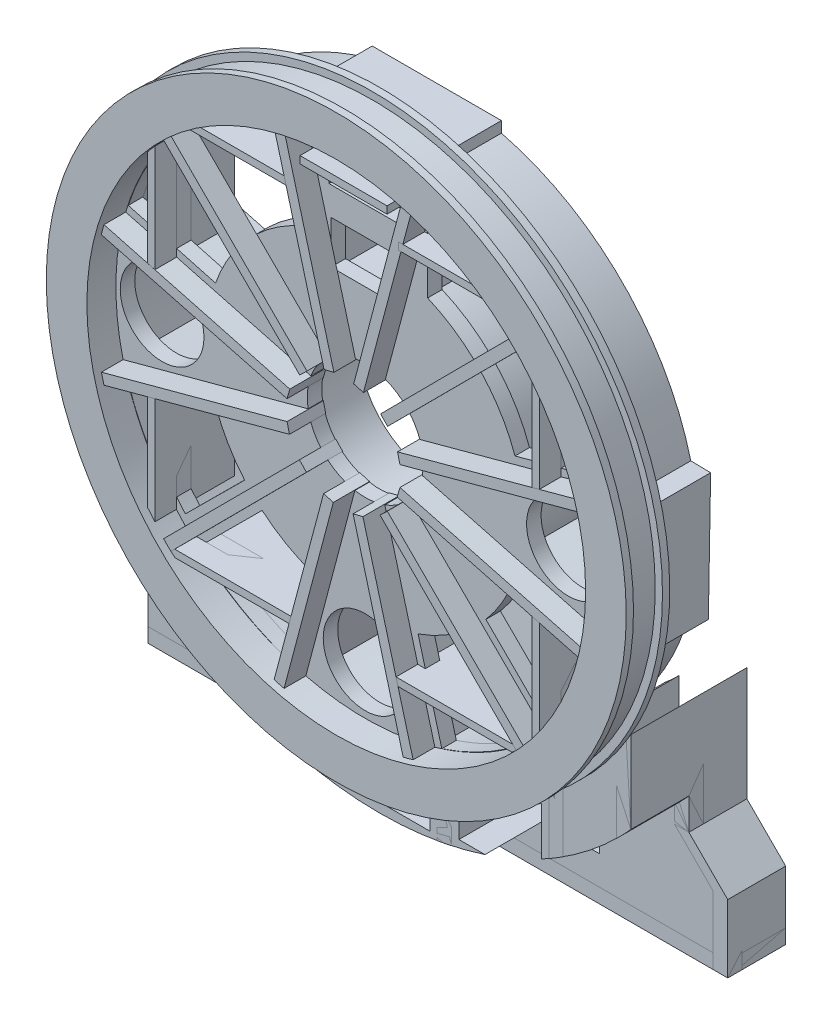
SolidWorks part; units mm, degrees
ref_plane "Front Plane" through (0, 0, 0) normal (0, 0, 1) x (1, 0, 0)
ref_plane "Top Plane" through (0, 0, 0) normal (0, 1, 0) x (1, 0, 0)
ref_plane "Right Plane" through (0, 0, 0) normal (1, 0, 0) x (0, 0, -1)
sketch "Sketch1" plane through (0, 0, 0) normal (0, 0, 1) x (1, 0, 0)
  circle A0 centre (0, 0) radius 200
extrude "Boss-Extrude1" add sketch "Sketch1" along normal blind 5
sketch "Sketch2" plane through (0, 0, 5) normal (0, 0, 1) x (1, 0, 0)
  circle A0 centre (0, 0) radius 195
extrude "Boss-Extrude2" add sketch "Sketch2" along normal blind 10
ref_plane "Plane1" through (0, 0, 15) normal (0, 0, 1) x (1, 0, 0)
mirror "Mirror2" about plane through (0, 0, 15) normal (0, 0, 1) of "Boss-Extrude2"
mirror "Mirror3" about plane through (0, 0, 15) normal (0, 0, 1) of "Boss-Extrude1"
sketch "Sketch4" plane through (0, 0, 0) normal (0, 0, 1) x (1, 0, 0)
  circle A0 centre (0, 0) radius 180
  circle A1 centre (0, 0) radius 172
extrude "Boss-Extrude3" add sketch "Sketch4" against normal blind 40
sketch "Sketch5" plane through (0, 0, 0) normal (0, 0, -1) x (-1, 0, 0)
  circle A0 centre (0, 0) radius 104.5
  circle A1 centre (0, 0) radius 96.5
sketch "Sketch6" plane through (0, 0, 0) normal (0, 0, -1) x (-1, 0, 0)
  circle A0 centre (0, 0) radius 40
extrude "Cut-Extrude1" cut sketch "Sketch6" against normal through all both and the other way through all
sketch "Sketch7" plane through (0, 0, 30) normal (0, 0, 1) x (1, 0, 0)
  circle A0 centre (0, 0) radius 172
  circle A1 centre (0, 0) radius 40 construction
extrude "Cut-Extrude2" cut sketch "Sketch7" against normal blind 20
sketch "Sketch8" plane through (0, 0, 0) normal (0, 0, -1) x (-1, 0, 0)
  line L1 (-226.8867, 0) -> (327.5333, 0) construction
  line L3 (10.3528, -38.637) -> (44.5169, -166.1392) construction
sketch "Sketch11" plane through (0, 0, 0) normal (0, 0, -1) x (-1, 0, 0)
  line L0 (0, 220.657) -> (0, -234.2087) construction
  line L1 (10.3528, -38.637) -> (44.5169, -166.1392) construction
  line L3 (13.739, -37.0329) -> (48.7398, -168.4842) construction
  line L6 (41.8584, -170.3245) -> (7.0358, -38.9499) construction
  line L8 (7.0358, -38.9499) -> (13.739, -37.0329)
  line L9 (7.0358, -38.9499) -> (41.8584, -170.3245)
  line L10 (13.739, -37.0329) -> (48.7398, -168.4842)
  line L11 (41.8584, -170.3245) -> (48.7398, -168.4842)
  dimension "D1" = 15
extrude "Boss-Extrude12" add sketch "Sketch11" along normal blind 40 and the other way blind 25
pattern_circular "CirPattern7" count 12 every 30 about axis through (0, 0, 0) along (0, 0, 1) of "Boss-Extrude12"
extrude "Boss-Extrude14" add sketch "Sketch5" along normal blind 40
sketch "Sketch16" plane through (0, 0, 0) normal (0, 0, -1) x (-1, 0, 0)
  circle A0 centre (0, 0) radius 63
  circle A2 centre (0, 0) radius 55
extrude "Boss-Extrude15" add sketch "Sketch16" along normal blind 40
sketch "Sketch17" plane through (0, 0, 0) normal (0, 0, -1) x (-1, 0, 0)
  circle A0 centre (0, 0) radius 55
  circle A1 centre (0, 0) radius 40
ref_plane "Plane3" through (0, 0, -40) normal (0, 0, -1) x (-1, 0, 0)
sketch "Sketch18" plane through (0, 0, -40) normal (0, 0, -1) x (-1, 0, 0)
  circle A1 centre (0, 0) radius 55
extrude "Cut-Extrude9" cut sketch "Sketch18" against normal blind 40
sketch "Sketch20" plane through (0, 0, 0) normal (0, 0, -1) x (-1, 0, 0)
  line L0 (-76.3832, 71.3152) -> (-124.0564, 119.1386)
  line L1 (76.2988, 71.4055) -> (124.1704, 119.0198)
  line L2 (-70.7313, 65.6455) -> (-47.0532, 41.8927)
  line L3 (70.6239, 65.7611) -> (46.8523, 42.1173)
  arc A0 (76.2988, 71.4055) -> (-76.3832, 71.3152) centre (0, 0) ccw
  arc A1 (124.1704, 119.0198) -> (-124.0564, 119.1386) centre (0, 0) ccw
  arc A2 (46.8523, 42.1173) -> (-47.0532, 41.8927) centre (0, 0) ccw
  arc A3 (70.6239, 65.7611) -> (-70.7313, 65.6455) centre (0, 0) ccw
extrude "Cut-Extrude13" cut sketch "Sketch20" along normal blind 40
sketch "Sketch21" plane through (0, 0, -40) normal (0, 0, -1) x (-1, 0, 0)
  line L0 (0, 245.7288) -> (0, -237.5415) construction
  line L1 (-138.1613, 239.3024) -> (0, 0) construction
  line L2 (0, 0) -> (159.1654, 275.6826) construction
  line L3 (-33.0054, 0) -> (-33.0054, 111.1117) construction
  dimension "D1" = 30
  dimension "D2" = 60
sketch "Sketch22" plane through (0, 0, -40) normal (0, 0, -1) x (-1, 0, 0)
  line L0 (25.0054, 0) -> (25.0054, 281.7628) construction
  line L1 (-25.0054, 0) -> (-25.0054, 250.3344) construction
  line L2 (-33.0054, 0) -> (-33.0054, 111.1117) construction
  line L3 (33.0054, 0) -> (33.0054, 272.1332) construction
  line L4 (-33.0054, 0) -> (-33.0054, 250.3344) construction
  point P11 (-25.0054, 48.987)
  point P12 (-513.0578, 150.8351)
  dimension "D1" = 8
sketch "Sketch25" plane through (0, 0, -40) normal (0, 0, -1) x (-1, 0, 0)
  line L0 (-30.0323, 46.0767) -> (-30.0323, 76.987)
  line L1 (-38.0323, 39.7309) -> (-38.0323, 76.987)
  line L2 (-38.0323, 76.987) -> (38, 76.987)
  line L3 (30, 46.0977) -> (30, 76.987)
  line L4 (-38, 66.987) -> (38, 66.987)
  line L8 (38, 39.7618) -> (38, 76.987)
  line L10 (-30.0323, 176.987) -> (-30.0323, 177.4769)
  line L12 (0, 245.7288) -> (0, -237.5415) construction
  line L13 (0, 130) -> (-38.0323, 130)
  line L16 (38, 130) -> (0, 130)
  line L20 (-38.0323, 76.987) -> (-38.0323, 175.9362)
  line L21 (38, 76.987) -> (38, 175.9432)
  line L22 (30, 76.987) -> (30, 177.4824)
  line L25 (-30.0323, 76.987) -> (-30.0323, 176.987)
  line L26 (-38.0323, 122) -> (38, 122)
  arc A0 (38, 175.9432) -> (-38.0323, 175.9362) centre (0, 0) ccw
  arc A1 (38, 39.7618) -> (30, 46.0977) centre (0, 0) ccw
  arc A2 (-30.0323, 46.0767) -> (-38.0323, 39.7309) centre (0, 0) ccw
  dimension "D1" = 8
  dimension "D4" = 8
  dimension "D2" = 8
extrude "Boss-Extrude18" add sketch "Sketch25" against normal blind 40
sketch "Sketch27" plane through (0, 0, 0) normal (0, 0, -1) x (-1, 0, 0)
  line L1 (-30.0323, 122) -> (30, 122)
  line L2 (-30.0323, 122) -> (-30.0323, 76.987)
  line L3 (-30.0323, 76.987) -> (30, 76.987)
  line L4 (30, 122) -> (30, 76.987)
  line L5 (-30.0323, 122) -> (30, 76.987) construction
  line L6 (-30.0323, 76.987) -> (30, 122) construction
  line L7 (-30.0323, 66.987) -> (30, 66.987)
  line L8 (-30.0323, 66.987) -> (-30.0323, 40)
  line L9 (-30.0323, 40) -> (30, 40)
  line L10 (30, 66.987) -> (30, 40)
  line L11 (-30.0323, 66.987) -> (30, 40) construction
  line L12 (-30.0323, 40) -> (30, 66.987) construction
  point P4 (-0.0161, 99.4935)
  point P11 (-0.0161, 53.4935)
extrude "Cut-Extrude15" cut sketch "Sketch27" along normal blind 40
ref_plane "Plane4" through (0, 0, -50) normal (0, 0, -1) x (-1, 0, 0)
sketch "Sketch30" plane through (0, 0, -50) normal (0, 0, -1) x (-1, 0, 0)
  line L0 (-38.0323, 97.3334) -> (-38.0323, 167.7425) construction
  line L1 (-38.0323, 130) -> (38, 130)
  line L2 (-38.0323, 130) -> (-38.0323, 167.7425)
  line L4 (38, 130) -> (38, 167.7498)
  arc A0 (38, 167.7498) -> (-38.0323, 167.7425) centre (0, 0) ccw
  point P4 (-0.0161, 151.6509)
extrude "Cut-Extrude16" cut sketch "Sketch30" against normal blind 35
ref_plane "Plane5" through (0, 0, -40) normal (0, 0, -1) x (-1, 0, 0)
sketch "Sketch31" plane through (0, 0, -40) normal (0, 0, -1) x (-1, 0, 0)
  line L0 (-38.0323, 167.7425) -> (-38.0323, 182.0805)
  line L1 (-43.8991, 172.6431) -> (-43.8991, 166.3035)
  line L2 (38, 182.0805) -> (38, 167.7498)
  line L3 (-43.8991, 182.0805) -> (45.1952, 182.0805)
  line L8 (-43.8991, 182.0805) -> (-43.8991, 172.6431)
  line L9 (-43.8991, 172.6431) -> (45.1952, 172.6431)
  line L10 (45.1952, 182.0805) -> (45.1952, 172.6431)
  line L11 (45.1952, 172.6431) -> (45.1952, 165.956)
  arc A0 (45.1952, 165.956) -> (-43.8991, 166.3035) centre (0, 0) ccw
  point P10 (-0.0193, 178.6973)
  point P11 (0.648, 177.3618)
extrude "Boss-Extrude19" add sketch "Sketch31" against normal blind 44 contours A0 L0 L9 L1 | L8 L9 L0 L3 | L0 L9 L2 L3 | A0 L2 L9 L0 | A0 L11 L9 L2 | L10 L3 L2 L9
sketch "Sketch32" plane through (0, 0, 0) normal (0, 0, 1) x (1, 0, 0)
  line L0 (0, 0) -> (-173.1406, -99.4798)
  line L1 (0, 0) -> (0, -390) construction
  line L2 (0, 0) -> (173.1482, -99.4666)
  line L3 (173.1482, -99.4666) -> (173.1482, -389.8428)
  line L4 (-173.1406, -99.4798) -> (-173.1406, -389.8428)
  line L5 (0.0076, -199.6845) -> (0, -390)
  line L6 (173.1482, -389.8428) -> (-173.1406, -389.8428)
  line L12 (125.8692, -389.8428) -> (126.5384, -128.0157)
  line L14 (39.5868, -389.8428) -> (39.5868, -195.7212)
  line L16 (49.5868, -389.8428) -> (49.5868, -173.0351)
  line L17 (39.5868, -389.8428) -> (39.5868, -175.593)
  line L19 (-39.4279, -389.8428) -> (-39.4279, -175.6287)
  line L21 (-49.4279, -389.8428) -> (-49.4279, -173.0806)
  line L24 (-116.5381, -389.8428) -> (-116.5381, -137.1819)
  line L26 (-126.5381, -389.8428) -> (-126.5381, -128.016)
  line L28 (116.0868, -389.8428) -> (116.733, -137.0161)
  arc A0 (-173.1406, -99.4798) -> (173.1482, -99.4666) centre (0, 0) ccw
  circle A1 centre (0, 0) radius 180
  point P15 (173.1482, -99.4666)
  point P16 (-173.1406, -99.4798)
extrude "Boss-Extrude20" add sketch "Sketch32" against normal blind 80 contours A0 L28 L6 L12 | A1 L28 A0 L12 | A1 L17 A0 L16 | A0 L14 L6 L16 | A1 L21 A0 L19 | A0 L21 L6 L19 | A1 L26 A0 L24 | A0 L26 L6 L24
sketch "Sketch33" plane through (0, 0, 0) normal (0, 0, -1) x (-1, 0, 0)
  line L2 (0, 0) -> (0, -342.4917) construction
  line L3 (-173.2051, -100) -> (-173.2051, -178.3656)
  line L5 (173.2051, -100) -> (173.2051, -178.6485)
  line L6 (190, -389.8428) -> (190, -205.4434)
  line L7 (-200, -205.1605) -> (-200, -389.8428)
  line L8 (200, -205.4434) -> (200, -389.8428)
  line L9 (-173.2051, -178.3656) -> (-200, -205.1605)
  line L10 (173.2051, -178.6485) -> (200, -205.4434)
  line L13 (190, -389.8428) -> (200, -389.8428)
  line L15 (-190, -389.8428) -> (-190, -205.1605)
  line L16 (-190, -205.1605) -> (-163.2051, -178.3656)
  line L17 (-163.2051, -178.3656) -> (-163.2051, -115.6032)
  line L19 (-190, -389.8428) -> (-200, -389.8428)
  line L20 (190, -205.4434) -> (163.2051, -178.6485)
  line L21 (163.2051, -178.6485) -> (163.2051, -115.6032)
  line L22 (-190, -389.8428) -> (190, -389.8428)
  arc A0 (-173.2051, -100) -> (173.2051, -100) centre (0, 0) ccw
extrude "Boss-Extrude21" add sketch "Sketch33" along normal blind 80 separate body contours A0 L3 L9 L7 L19 L15 L16 L17 | A0 L21 L20 L6 L13 L8 L10 L5
sketch "Sketch34" plane through (0, 0, 0) normal (0, 0, -1) x (-1, 0, 0)
  line L0 (-200, -389.8428) -> (200, -389.8428)
  line L1 (200, -389.8428) -> (200, -205.4434)
  line L2 (200, -205.4434) -> (173.2051, -178.6485)
  line L3 (173.2051, -178.6485) -> (173.2051, -100)
  line L4 (-200, -389.8428) -> (-200, -205.1605)
  line L5 (-200, -205.1605) -> (-173.2051, -178.3656)
  line L6 (-173.2051, -178.3656) -> (-173.2051, -100)
  circle A0 centre (0, 0) radius 200
  circle A1 centre (0, 0) radius 200
extrude "Boss-Extrude26" add sketch "Sketch34" along normal blind 50 separate body contours A0 L6 L5 L4 L0 L1 L2 L3
ref_plane "Plane8" through (0, 0, 0) normal (-1, 0, 0) x (0, 0, 1)
sketch "Sketch38" plane through (0, 0, 0) normal (-1, 0, 0) x (0, 0, 1)
  line L0 (0, -200) -> (197.9741, -200) construction
  line L1 (30, -200) -> (30, -304.3172) construction
  line L2 (30, -200) -> (0, -200) construction
  line L3 (0, -178.3656) -> (0, -205.1605) construction
  line L4 (0, -200) -> (0, -302.6251) construction
  line L5 (0, -205.1605) -> (0, -389.8428) construction
  line L6 (0, -200) -> (-40, -166.436) construction
  line L7 (-50, -205.1605) -> (-40, -205.1605) construction
  line L8 (-80, -205.1605) -> (0, -205.1605) construction
  line L9 (-40, -205.1605) -> (-40, -166.436) construction
  line L10 (0, 0) -> (-40, -166.436)
  line L11 (-40, -166.436) -> (-40, 0) construction
  line L13 (0, 0) -> (-40, 0) construction
  point P17 (-40, -166.436)
  dimension "D2" = 166.436
  dimension "D1" = 50
sketch "Sketch39" plane through (0, 0, 10) normal (0, 0, 1) x (1, 0, 0)
  line L0 (-233.56, 0) -> (-438.1523, 0)
  line L1 (233.56, 0) -> (438.1523, 0)
  arc A0 (-233.56, 0) -> (233.56, 0) centre (0, 0) ccw
  arc A1 (-438.1523, 0) -> (438.1523, 0) centre (0, 0) ccw
extrude "Cut-Extrude17" cut sketch "Sketch39" against normal blind 40
ref_plane "Plane9" through (0, 0, 30) normal (0, 0, 1) x (1, 0, 0)
sketch "Sketch41" plane through (0, 0, 30) normal (0, 0, 1) x (1, 0, 0)
  line L0 (-306.4353, 0) -> (417.3108, 0) construction
  line L1 (0, 247.8182) -> (0, -475.0549) construction
  line L2 (0, -172) -> (470.7399, -172) construction
  line L3 (470.7399, -172) -> (-364.2612, -172) construction
  line L4 (0, -172) -> (0, -252) construction
  line L5 (-200, -389.8428) -> (200, -389.8428)
  line L6 (-200, -389.8428) -> (-200, -252)
  line L7 (200, -389.8428) -> (200, -252)
  line L8 (-200, -252) -> (200, -252)
  circle A0 centre (0, 0) radius 172 construction
  dimension "D1" = 0
extrude "Cut-Extrude18" cut sketch "Sketch41" against normal through all
sketch "Sketch42" plane through (0, 0, -40) normal (0, 0, -1) x (-1, 0, 0)
  line L0 (200, -252) -> (-200, -252)
  line L1 (200, -252) -> (200, -242)
  line L2 (-200, -252) -> (-200, -242)
  line L3 (200, -242) -> (-200, -242)
extrude "Boss-Extrude29" add sketch "Sketch42" along normal blind 40 and the other way blind 10 separate body
ref_plane "Plane10" through (0, 0, 0) normal (0, 0, -1) x (-1, 0, 0)
sketch "Sketch43" plane through (0, 0, 0) normal (0, 0, -1) x (-1, 0, 0)
  line L0 (-291.6105, 0) -> (344.5212, 0) construction
  line L1 (0, 0) -> (-368.6851, 0) construction
  line L2 (0, 0) -> (175.6246, 0) construction
  line L3 (200, 0) -> (200, 184.7371) construction
  line L5 (187.4158, 44.3236) -> (187.4158, -44.1213)
  line L6 (187.4158, 44.3236) -> (170.0068, 44.3236)
  line L10 (187.4158, -44.1213) -> (168.5926, -44.1213)
  line L13 (-186.6526, -44.5312) -> (-188.1962, 43.9088)
  line L14 (-186.6526, -44.5312) -> (-169.2463, -44.2274)
  line L15 (-188.1962, 43.9088) -> (-169.3759, 44.2373)
  line L16 (0, 0) -> (-180, 0) construction
  line L17 (187.4158, 0) -> (200, 0) construction
  arc A0 (170.0068, 44.3236) -> (168.5926, -44.1213) centre (17.8637, 2.5225) cw
  arc A1 (-169.2463, -44.2274) -> (-169.3759, 44.2373) centre (-17.8572, 0.2269) cw
  arc A2 (-43.8991, 174.5648) -> (-126.5384, -128.0157) centre (0, 0) ccw construction
  point P13 (-187.4244, -0.3112)
  point P20 (-175.6368, 0)
  dimension "D4" = 88.44
  dimension "D1" = 0
  dimension "D2" = 0
  dimension "D3" = 11.7912
  dimension "D5" = 187.4244
  dimension "D6" = 187.4158
extrude "Boss-Extrude31" add sketch "Sketch43" along normal blind 40
sketch "Sketch45" plane through (0, 0, -50) normal (0, 0, -1) x (-1, 0, 0)
  line L0 (205, -226.9042) -> (205, 0)
  line L1 (205, -237.3602) -> (205, -216.3758)
  line L2 (54.4279, -222) -> (111.5381, -222)
  line L3 (111.5381, -172.0007) -> (111.5381, -222)
  line L4 (54.4279, -197.6426) -> (54.4279, -222)
  line L5 (116.5381, -252) -> (116.5381, -137.1819) construction
  line L6 (49.4279, -252) -> (49.4279, -173.0806) construction
  line L7 (200, -242) -> (-200, -242) construction
  line L8 (-39.5868, -252) -> (-39.5868, -175.593) construction
  line L10 (-34.5868, -202.0613) -> (-34.5868, -227)
  line L11 (-34.5868, -227) -> (34.4279, -227)
  line L12 (34.4279, -202.0884) -> (34.4279, -227)
  line L13 (39.4279, -252) -> (39.4279, -175.6287) construction
  line L14 (-49.5868, -252) -> (-49.5868, -173.0351) construction
  line L16 (-111.5158, -172.0152) -> (-111.5158, -222)
  line L17 (-111.5158, -222) -> (-54.5868, -222)
  line L18 (-54.5868, -197.5988) -> (-54.5868, -222)
  line L19 (-116.4391, -252) -> (-116.733, -137.0161) construction
  circle A0 centre (0, 0) radius 205
  dimension "D1" = 5
  dimension "D4" = 15
  dimension "D2" = 5
  dimension "D3" = 20
  dimension "D5" = 5
  dimension "D6" = 5
  dimension "D8" = 20
  dimension "D9" = 5
  dimension "D10" = 5
extrude "Cut-Extrude19" cut sketch "Sketch45" against normal through all contours A0 L10 L11 L12 | A0 L4 L2 L3 | A0 L16 L17 L18
sketch "Sketch48" plane through (0, 0, -30) normal (0, 0, 1) x (1, 0, 0)
  line L0 (-200, -252) -> (200, -252)
  line L1 (200, -252) -> (190, -252) construction
  line L2 (200, -252) -> (200, -155.8788)
  line L4 (200, -155.8788) -> (173.9312, -155.8788)
  line L5 (-200, -155.8788) -> (-200, -252)
  line L6 (-173.9312, -155.8788) -> (-200, -155.8788)
  arc A0 (-173.9312, -155.8788) -> (173.9312, -155.8788) centre (0, 0) ccw
extrude "Cut-Extrude20" cut sketch "Sketch48" against normal blind 10
sketch "Sketch49" plane through (0, 0, 10) normal (0, 0, 1) x (1, 0, 0)
  line L0 (0, 274.6736) -> (0, -309.1586) construction
  point P0 (0, 0)
ref_plane "Plane21" through (0, 0, 10) normal (0, -1, 0) x (-1, 0, 0)
sketch "Sketch50" plane through (0, 0, 0) normal (0, 0, -1) x (-1, 0, 0)
  line L0 (0, 0) -> (0, 308.6024) construction
  line L1 (-130.0788, -43.688) -> (-103.2243, -36.5376)
  line L2 (-109.5485, -121.5564) -> (-41.3956, -121.5564)
  line L3 (-116.2046, -126.5564) -> (-42.7498, -126.5564)
  line L5 (135.0788, -45.0194) -> (135.0788, -106.0634)
  line L7 (-36.2154, -121.5564) -> (-37.5696, -126.5564)
  line L8 (-30.3739, -99.9884) -> (-48.0248, -165.1594) construction
  line L9 (-48.0248, -165.1594) -> (-30.3739, -99.9884) construction
  line L10 (-163.9188, -52.6984) -> (-103.2243, -36.5376)
  line L11 (42.7498, -126.5564) -> (52.7967, -163.6522)
  line L12 (116.2046, -126.5564) -> (42.7498, -126.5564)
  line L13 (-163.5429, -52.5983) -> (-135.0788, -45.0194)
  line L14 (163.5429, -52.5983) -> (135.0788, -45.0194)
  line L15 (-42.7498, -126.5564) -> (-52.7967, -163.6522)
  line L16 (-36.4398, -103.2588) -> (-51.4991, -158.8611)
  line L17 (-36.4398, -103.2588) -> (-41.3956, -121.5564)
  line L18 (-109.5485, -121.5564) -> (-71.126, -83.2547)
  line L19 (109.5485, -121.5564) -> (71.126, -83.2547)
  line L20 (109.5485, -121.5564) -> (41.3956, -121.5564)
  line L21 (36.4398, -103.2588) -> (41.3956, -121.5564)
  line L22 (130.0788, -43.688) -> (130.0788, -104.7306)
  line L23 (130.0788, -43.688) -> (103.2243, -36.5376)
  line L24 (-130.0788, -43.688) -> (-130.0788, -104.7306)
  line L25 (-135.0788, -45.0194) -> (-135.0788, -106.0634)
  line L26 (124.0301, -111.8282) -> (83.1873, -71.2049)
  line L28 (-130.0739, 43.7024) -> (-103.2588, 36.4398)
  line L30 (-127.6964, -115.4748) -> (-79.8248, -67.8605)
  line L31 (-124.0301, -111.8282) -> (-83.1873, -71.2049)
  line L32 (-43.0323, 139.1734) -> (-43.0323, 166.4817)
  line L33 (-130.0739, 43.7024) -> (-130.0739, 104.7368)
  line L34 (-135.0739, 45.0566) -> (-135.0739, 106.485)
  line L35 (135.0739, 45.0566) -> (135.0739, 106.485)
  line L38 (163.4513, 52.7423) -> (135.0739, 45.0566)
  line L39 (-43.0323, 97.3334) -> (-43.0323, 167.7425)
  line L40 (-43.0323, 139.1734) -> (-100.8346, 139.1734)
  line L41 (-43.0323, 134.1734) -> (-99.4308, 134.1734)
  line L42 (-43.0323, 100.69) -> (-43.0323, 134.1734)
  line L43 (43.0323, 139.1734) -> (100.8346, 139.1734)
  line L44 (-163.8523, 52.8509) -> (-98.6813, 35.2001)
  line L46 (-163.4513, 52.7423) -> (-135.0739, 45.0566)
  line L47 (43.0323, 139.1734) -> (43.0323, 166.4817)
  line L48 (43.0323, 100.69) -> (43.0323, 134.1734)
  line L49 (43.0323, 134.1734) -> (99.4308, 134.1734)
  line L50 (130.0739, 43.7024) -> (130.0739, 104.7368)
  line L51 (130.0739, 43.7024) -> (103.2588, 36.4398)
  line L53 (23.64, 85.845) -> (-23.64, 85.845)
  line L54 (23.64, 85.845) -> (23.64, 115.535)
  line L55 (23.64, 115.535) -> (-23.64, 115.535)
  line L56 (-23.64, 85.845) -> (-23.64, 115.535)
  line L57 (23.64, 85.845) -> (-23.64, 115.535) construction
  line L58 (23.64, 115.535) -> (-23.64, 85.845) construction
  line L59 (30, 130) -> (-30.0323, 130) construction
  line L62 (-25.0323, 135) -> (25, 135)
  line L63 (-25.0323, 135) -> (-25.0323, 151.73)
  line L65 (-25.0323, 151.73) -> (25, 151.73)
  line L66 (25, 135) -> (25, 151.73)
  line L67 (-30.0323, 169.3578) -> (-30.0323, 130) construction
  line L68 (30, 169.3635) -> (30, 130) construction
  line L69 (-25.0323, 156.73) -> (25, 156.73)
  line L70 (-25.0323, 156.73) -> (-25.0323, 167.6)
  line L71 (25, 156.73) -> (25, 167.6)
  line L72 (25, 167.6) -> (-25.0323, 167.6)
  circle A0 centre (-140.1186, 0) radius 28.87
  circle A1 centre (140.1186, 0) radius 28.87
  arc A2 (163.5429, -52.5983) -> (135.0788, -106.0634) centre (-2.6935, 1.5943) cw
  arc A3 (-163.5429, -52.5983) -> (-135.0788, -106.0634) centre (2.6935, 1.5943) ccw
  arc A4 (-103.2243, -36.5376) -> (-79.9494, -74.822) centre (0, 0) ccw
  arc A5 (-103.2243, -36.5376) -> (-83.1873, -71.2049) centre (0, 0) ccw
  arc A6 (130.0788, -104.7306) -> (124.0301, -111.8282) centre (0, 0) cw
  arc A7 (-130.0788, -104.7306) -> (-124.0301, -111.8282) centre (0, 0) ccw
  arc A8 (-116.2046, -126.5564) -> (-52.7967, -163.6522) centre (2.8348, 4.1784) ccw
  arc A9 (116.2046, -126.5564) -> (52.7967, -163.6522) centre (-2.8348, 4.1784) cw
  arc A10 (-115.6752, -120.4502) -> (-51.4991, -158.8611) centre (0, 0) ccw
  arc A11 (-74.7274, -80.0379) -> (-36.4398, -103.2588) centre (0, 0) ccw
  arc A12 (71.126, -83.2547) -> (36.4398, -103.2588) centre (0, 0) cw
  arc A13 (-71.126, -83.2547) -> (-36.4398, -103.2588) centre (0, 0) ccw
  arc A14 (103.2243, -36.5376) -> (83.1873, -71.2049) centre (0, 0) cw
  arc A15 (165.2053, 47.8667) -> (-165.1594, 48.0248) centre (0, 0) ccw construction
  arc A17 (-135.0739, 106.485) -> (-163.4513, 52.7423) centre (3.0343, -0.8029) ccw
  arc A18 (-100.8346, 139.1734) -> (-43.0323, 166.4817) centre (9.05, -18.5867) cw
  arc A19 (-39.852, 101.9905) -> (-104.7725, 31.8272) centre (0, 0) ccw
  arc A20 (-43.0323, 100.69) -> (-103.2588, 36.4398) centre (0, 0) ccw
  arc A21 (135.0739, 106.485) -> (163.4513, 52.7423) centre (-3.0343, -0.8029) cw
  arc A22 (100.8346, 139.1734) -> (43.0323, 166.4817) centre (-9.05, -18.5867) ccw
  arc A23 (-99.4308, 134.1734) -> (-130.0739, 104.7368) centre (0, 0) ccw
  arc A24 (99.4308, 134.1734) -> (130.0739, 104.7368) centre (0, 0) cw
  arc A25 (43.0323, 100.69) -> (103.2588, 36.4398) centre (0, 0) cw
  circle A27 centre (0, -138.389) radius 28.98
  point P45 (-132.5788, -39.1795)
  point P98 (0, 100.69)
  dimension "D4" = 57.74
  dimension "D5" = 5
  dimension "D8" = 29.69
  dimension "D9" = 47.28
  dimension "D10" = 5
  dimension "D12" = 5
  dimension "D11" = 5
  dimension "D13" = 16.73
  dimension "D15" = 10.87
  dimension "D1" = 5
  dimension "D2" = 5
  dimension "D3" = 5
  dimension "D6" = 5
  dimension "D7" = 5
  dimension "D14" = 5
extrude "Cut-Extrude21" cut sketch "Sketch50" against normal blind 10.1 contours L41 A23 L33 L28 A20 L42 | A18 L40 L32 | L43 A22 L47 | L56 L53 L54 L55 | L62 L66 L65 L63 | L71 L72 L70 L69 | L48 A25 L51 L50 A24 L49 | A21 L35 L38 | A1 | A0 | L34 A17 L46 | L13 A3 L25 | L24 A7 L31 A5 L1 | A13 L18 L2 L17 | L3 A8 L15 | A9 L12 L11 | L19 A12 L21 L20 | L23 A14 L26 A6 L22 | A2 L14 L5 | A27
sketch "Sketch51" plane through (0, 0, 0) normal (0, 0, -1) x (-1, 0, 0)
  line L0 (-135.0788, -45.0194) -> (-135.0788, -106.0634)
  line L1 (-135.0788, -45.0194) -> (-135.0788, -39.8452)
  line L2 (-165.2053, -47.8667) -> (-99.9524, -30.4922) construction
  line L3 (-130.0788, -43.688) -> (-130.0788, -38.5138)
  line L4 (-130.0788, -38.5138) -> (-135.0788, -39.8452)
  line L5 (-130.0788, -43.688) -> (-130.0788, -112.0521)
  line L6 (-135.0788, -106.0634) -> (-130.0788, -112.0521)
  line L7 (-109.5485, -121.5564) -> (-116.6307, -121.5564)
  line L8 (-119.1386, -124.0564) -> (-71.3152, -76.3832) construction
  line L9 (-116.6307, -121.5564) -> (-119.1386, -124.0564)
  line L10 (-119.1386, -124.0564) -> (-116.2046, -126.5564)
  line L11 (-116.2046, -126.5564) -> (-37.5696, -126.5564)
  line L12 (-48.0248, -165.1594) -> (-30.3739, -99.9884) construction
  line L13 (-37.5696, -126.5564) -> (-36.2154, -121.5564)
  line L14 (-30.3739, -99.9884) -> (-48.0248, -165.1594) construction
  line L15 (-36.2154, -121.5564) -> (-109.5485, -121.5564)
  line L16 (-135.0739, 106.485) -> (-135.0739, 39.8765)
  line L17 (-165.1594, 48.0248) -> (-99.9884, 30.3739) construction
  line L18 (-135.0739, 39.8765) -> (-130.0788, 38.5236)
  line L19 (-130.0788, 38.5236) -> (-130.0788, 112.5322)
  line L20 (-130.0788, 112.5322) -> (-135.0739, 106.485)
  line L21 (-99.4308, 134.1734) -> (-38.0323, 134.1734)
  line L22 (-38.0323, 97.3334) -> (-38.0323, 167.7425) construction
  line L24 (-43.0323, 139.1734) -> (-100.8346, 139.1734) construction
  line L25 (-99.4308, 139.1734) -> (-38.0323, 139.1734)
  line L26 (-38.0323, 139.1734) -> (-38.0323, 134.1734)
  line L27 (-99.4308, 134.1734) -> (-107.6173, 134.1734)
  line L28 (-107.6173, 134.1734) -> (-100.8346, 139.1734)
  line L29 (-100.8346, 139.1734) -> (-99.4308, 139.1734)
  line L30 (0, 0) -> (0, 346.3243) construction
  line L31 (37.5696, -126.5564) -> (36.2154, -121.5564)
  line L32 (116.2046, -126.5564) -> (37.5696, -126.5564)
  line L33 (119.1386, -124.0564) -> (116.2046, -126.5564)
  line L34 (116.6307, -121.5564) -> (119.1386, -124.0564)
  line L35 (109.5485, -121.5564) -> (116.6307, -121.5564)
  line L36 (36.2154, -121.5564) -> (109.5485, -121.5564)
  line L37 (99.4308, 134.1734) -> (107.6173, 134.1734)
  line L38 (107.6173, 134.1734) -> (100.8346, 139.1734)
  line L39 (100.8346, 139.1734) -> (99.4308, 139.1734)
  line L40 (99.4308, 139.1734) -> (38.0323, 139.1734)
  line L41 (38.0323, 139.1734) -> (38.0323, 134.1734)
  line L42 (99.4308, 134.1734) -> (38.0323, 134.1734)
  line L43 (130.0788, 38.5236) -> (130.0788, 112.5322)
  line L44 (135.0739, 39.8765) -> (130.0788, 38.5236)
  line L45 (135.0739, 106.485) -> (135.0739, 39.8765)
  line L46 (130.0788, 112.5322) -> (135.0739, 106.485)
  line L47 (130.0788, -43.688) -> (130.0788, -112.0521)
  line L48 (135.0788, -106.0634) -> (130.0788, -112.0521)
  line L49 (135.0788, -45.0194) -> (135.0788, -106.0634)
  line L50 (135.0788, -45.0194) -> (135.0788, -39.8452)
  line L51 (130.0788, -38.5138) -> (135.0788, -39.8452)
  line L52 (130.0788, -43.688) -> (130.0788, -38.5138)
  line L53 (-25.0323, 151.73) -> (30, 151.73)
  line L54 (30, 130) -> (30, 169.3635) construction
  line L55 (-30.0323, 156.73) -> (30, 156.73)
  line L56 (-30.0323, 169.3578) -> (-30.0323, 130) construction
  line L57 (30, 156.73) -> (30, 151.73)
  line L58 (-25.0323, 151.73) -> (-30.0323, 151.73)
  line L59 (-30.0323, 151.73) -> (-30.0323, 156.73)
  arc A1 (-38.0323, 167.7425) -> (-135.0739, 106.485) centre (0, 0) ccw construction
extrude "Boss-Extrude32" add sketch "Sketch51" along normal blind 30 and the other way blind 25 separate body
